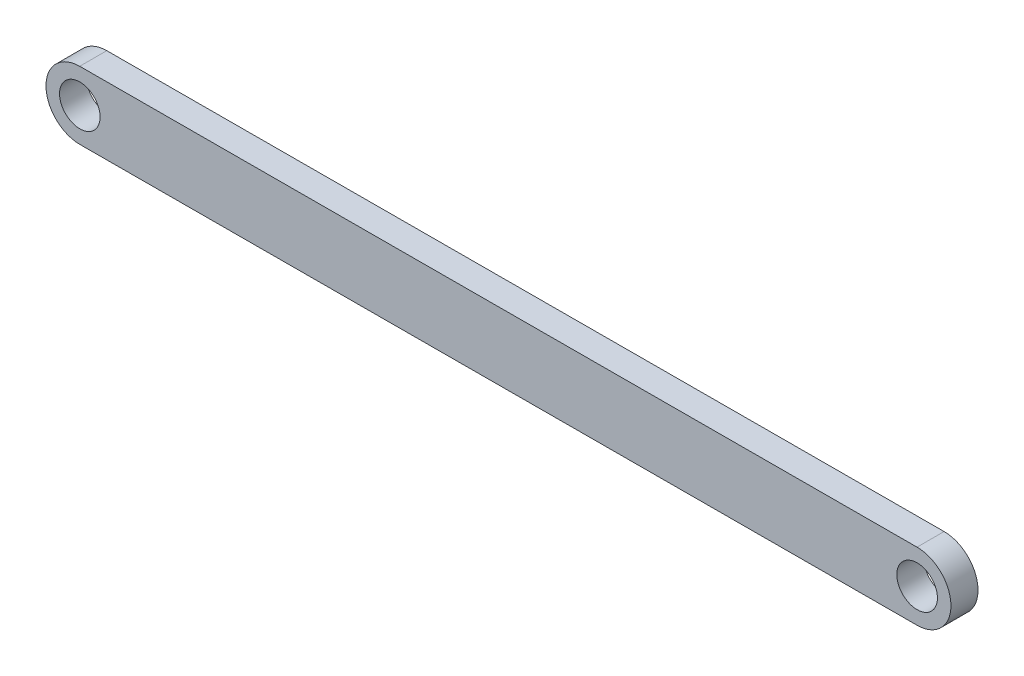
SolidWorks part; units mm, degrees
ref_plane "Front Plane" through (0, 0, 0) normal (0, 0, 1) x (1, 0, 0)
ref_plane "Top Plane" through (0, 0, 0) normal (0, 1, 0) x (1, 0, 0)
ref_plane "Right Plane" through (0, 0, 0) normal (1, 0, 0) x (0, 0, -1)
sketch "Sketch1" plane through (0, 0, 0) normal (0, 0, 1) x (1, 0, 0)
  line L0 (-31.0634, -0.1728) -> (30.8366, -0.0092) construction
  line L1 (-31.0701, 2.3272) -> (30.8299, 2.4908)
  line L2 (-31.0568, -2.6728) -> (30.8432, -2.5092)
  arc A0 (-31.0701, 2.3272) -> (-31.0568, -2.6728) centre (-31.0634, -0.1728) ccw
  arc A1 (30.8432, -2.5092) -> (30.8299, 2.4908) centre (30.8366, -0.0092) ccw
  circle A2 centre (-31.0634, -0.1728) radius 1.5
  circle A3 centre (30.8366, -0.0092) radius 1.5
  point P2 (-0.1134, -0.091)
  dimension "D3" = 3
  dimension "D4" = 3
  dimension "D1" = 61.9
  dimension "D2" = 5
extrude "Boss-Extrude1" add sketch "Sketch1" along normal blind 2
